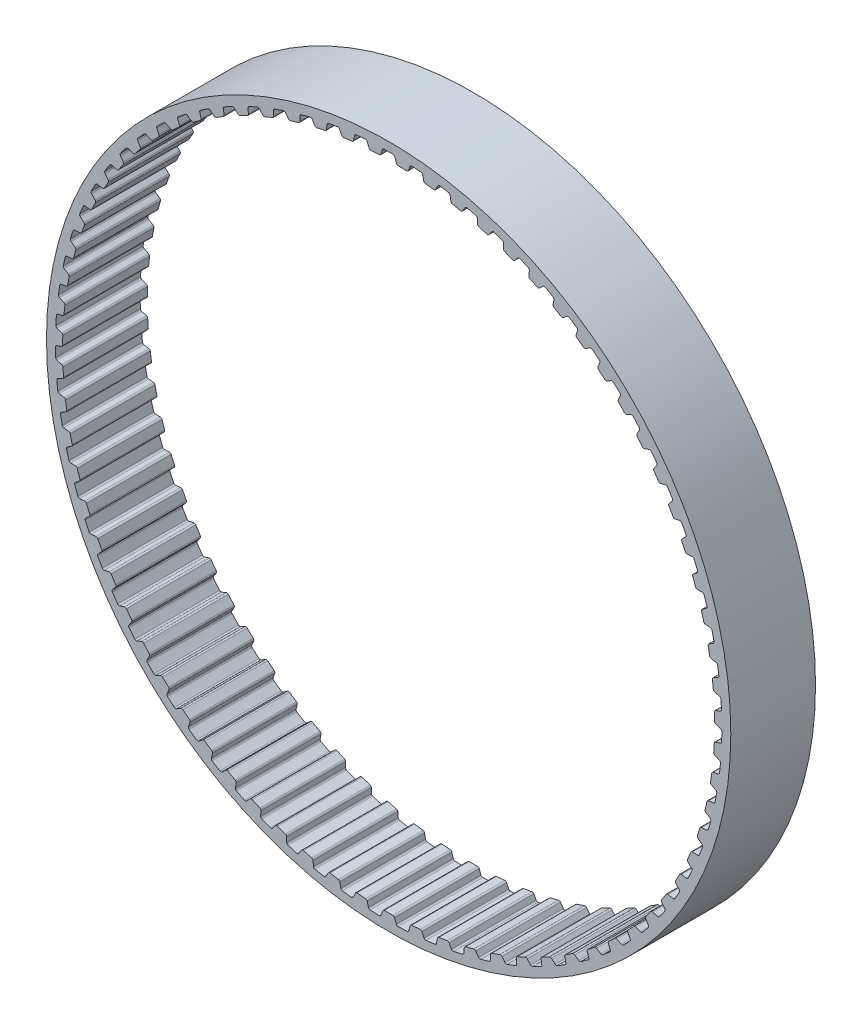
SolidWorks part; units mm, degrees
ref_plane "Front Plane" through (0, 0, 0) normal (0, 0, 1) x (1, 0, 0)
ref_plane "Top Plane" through (0, 0, 0) normal (0, 1, 0) x (1, 0, 0)
ref_plane "Right Plane" through (0, 0, 0) normal (1, 0, 0) x (0, 0, -1)
sketch "Sketch1" plane through (0, 0, 0) normal (0, 0, 1) x (1, 0, 0)
  line L0 (0, 0) -> (-0.9668, 23.0681) construction
  line L1 (0, 0) -> (0.9668, 23.0681) construction
  line L2 (0.9668, 23.0681) -> (-0.9668, 23.0681) construction
  line L3 (0.9668, 23.0681) -> (-0.9668, 23.0681) construction
  circle A0 centre (0, 0) radius 24.2314
  circle A1 centre (0, 0) radius 23.0884
  circle A2 centre (0, 0) radius 23.5964 construction
  dimension "OD" = 48.4627
  dimension "Angle Distance" = 4.8
  dimension "hs" = 1.143
  dimension "ht" = 0.508
sketch "Sketch4" plane through (0, 0, 0) normal (0, 0, 1) x (1, 0, 0)
  circle A0 centre (0, 0) radius 23.0884 construction
  circle A1 centre (0, 0) radius 24.2314 construction
  circle A2 centre (0, 0) radius 23.0884
  circle A3 centre (0, 0) radius 24.2314
extrude "Boss-Extrude1" add sketch "Sketch4" along normal mid plane 6
sketch "Sketch2" plane through (0, 0, 0) normal (0, 0, 1) x (1, 0, 0)
  line L1 (0, 24.2314) -> (0, 0) construction
  line L2 (-1.015, 23.3386) -> (1.015, 23.3386) construction
  line L4 (-0.5776, 23.0844) -> (-1.3561, 23.0518)
  line L5 (-0.5776, 23.0844) -> (-0.4163, 23.5927)
  line L6 (-1.3561, 23.0518) -> (-1.5593, 23.5448)
  line L7 (0, 0) -> (-0.9668, 23.0681) construction
  line L8 (-0.4163, 23.5927) -> (-1.5593, 23.5448) construction
  line L9 (0.4163, 23.5927) -> (1.5593, 23.5448) construction
  line L10 (1.3561, 23.0518) -> (1.5593, 23.5448)
  line L11 (0.5776, 23.0844) -> (0.4163, 23.5927)
  line L12 (0.5776, 23.0844) -> (1.3561, 23.0518)
  line L13 (0, 0) -> (9.2729, 22.3869) construction
  line L14 (-1.015, 23.3386) -> (-3.0373, 23.1623) construction
  line L15 (-2.0262, 23.2504) -> (0, 0) construction
  line L16 (-3.0373, 23.1623) -> (-3.0019, 22.8924) construction
  circle A0 centre (0, 0) radius 23.5964 construction
  circle A1 centre (0, 0) radius 23.5964
  circle A2 centre (0, 0) radius 23.3386 construction
  circle A4 centre (0, 0) radius 24.2314 construction
  circle A5 centre (0, 0) radius 23.0884 construction
  point P16 (-0.4969, 23.3386)
  point P20 (0, 23.3386)
  dimension "D1" = 22.5
  dimension "bt" = 1.143
  dimension "b" = 40
  dimension "Pitch" = 2.03
sketch "Sketch3" plane through (0, 0, 0) normal (0, 0, 1) x (1, 0, 0)
  line L0 (-0.6687, 23.0787) -> (0.6687, 23.0787)
  line L2 (-0.5776, 23.0844) -> (-0.4163, 23.5927) construction
  line L3 (0.5776, 23.0844) -> (0.4163, 23.5927) construction
  line L5 (-0.5513, 23.1672) -> (-0.444, 23.5055)
  line L7 (0.5513, 23.1672) -> (0.444, 23.5055)
  arc A0 (0.5513, 23.1672) -> (0.6687, 23.0787) centre (0.6723, 23.2056) ccw
  circle A1 centre (0, 0) radius 23.5964 construction
  arc A2 (0.3247, 23.5941) -> (-0.3247, 23.5941) centre (0, 0) ccw
  arc A3 (-0.5513, 23.1672) -> (-0.6687, 23.0787) centre (-0.6723, 23.2056) cw
  arc A4 (0.444, 23.5055) -> (0.3247, 23.5941) centre (0.3229, 23.4671) ccw
  arc A5 (-0.444, 23.5055) -> (-0.3247, 23.5941) centre (-0.3229, 23.4671) cw
  circle A6 centre (0, 0) radius 23.0884 construction
  arc A7 (-0.6687, 23.0787) -> (0.6687, 23.0787) centre (0, 0) ccw construction
  dimension "ra" = 0.127
  dimension "rr" = 0.127
extrude "Cut-Extrude1" cut sketch "Sketch3" against normal mid plane 6
pattern_circular "CirPattern1" count 75 over 360 about axis through (0, 0, 0) along (0, 0, 1) of "Cut-Extrude1"
equation "\"D1@Cut-Extrude1\" = \"Width@Boss-Extrude1\""
